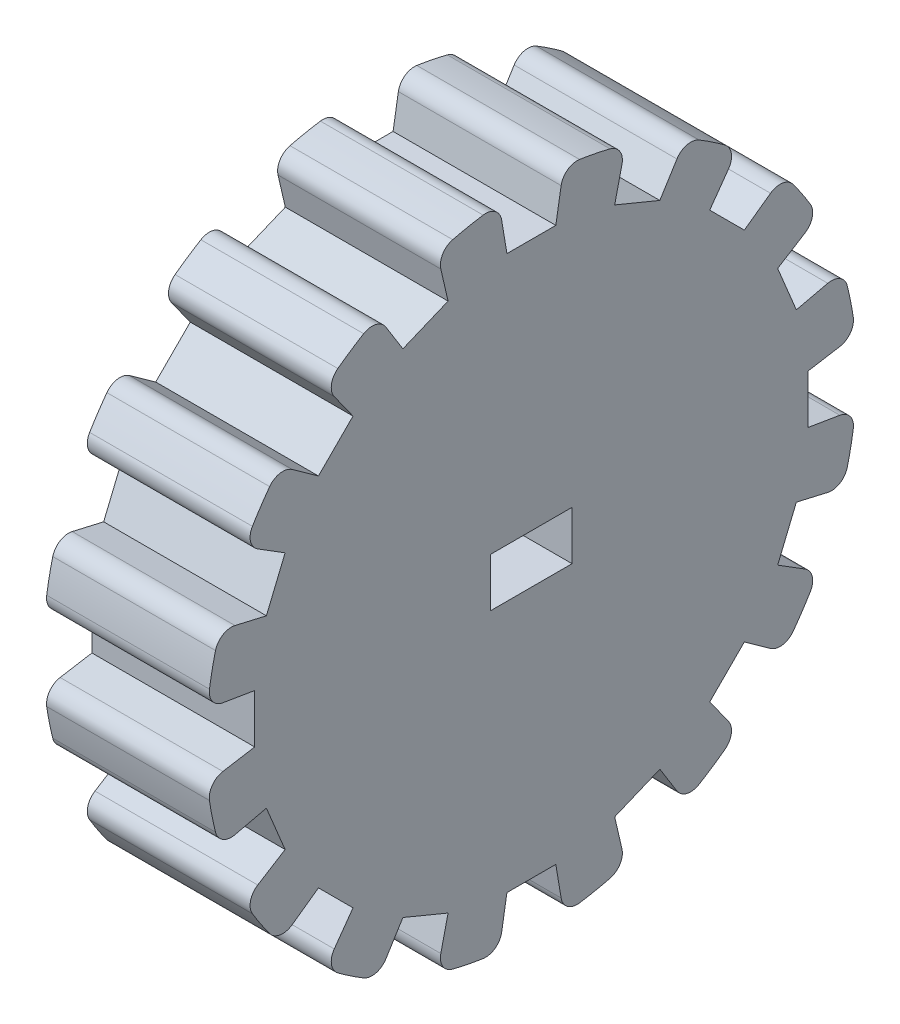
SolidWorks part; units mm, degrees
ref_plane "Front Plane" through (0, 0, 0) normal (0, 0, 1) x (1, 0, 0)
ref_plane "Top Plane" through (0, 0, 0) normal (0, 1, 0) x (1, 0, 0)
ref_plane "Right Plane" through (0, 0, 0) normal (1, 0, 0) x (0, 0, -1)
sketch "Sketch1" plane through (0, 0, 0) normal (0, 0, 1) x (1, 0, 0)
  line L0 (0, 0) -> (-34.486, 0) construction
  line L1 (0, 0) -> (-10, 0)
  line L2 (-10, 0) -> (-10, 5)
  line L3 (-10, 10) -> (-10, 5)
  line L4 (0, 20) -> (0, 5)
  line L6 (-10, 10) -> (-10, 20)
  line L7 (-10, 20) -> (0, 20)
  line L12 (0, 5) -> (0, 0)
  dimension "D1" = 20
  dimension "D2" = 20
  dimension "D3" = 10
  dimension "D5" = 5
  dimension "D6" = 10
revolve "Revolve1" add sketch "Sketch1" angle 360 about L0
sketch "Sketch4" plane through (-10, 0, 0) normal (-1, 0, 0) x (0, 0, 1)
  line L1 (2.5, -1.5) -> (-2.5, -1.5)
  line L6 (2.5, -1.5) -> (2.5, 1.5)
  line L7 (2.5, 1.5) -> (-2.5, 1.5)
  line L8 (-2.5, -1.5) -> (-2.5, 1.5)
  line L9 (2.5, -1.5) -> (-2.5, 1.5) construction
  line L10 (2.5, 1.5) -> (-2.5, -1.5) construction
  point P0 (0, 0)
  point P3 (0, 0)
  point P8 (0, 0)
  dimension "D1" = 3
  dimension "D2" = 5
extrude "Cut-Extrude2" cut sketch "Sketch4" against normal blind 10
sketch "Sketch5" plane through (0, 0, 0) normal (1, 0, 0) x (0, 0, -1)
  line L0 (-2.502, 23) -> (2.502, 23)
  line L1 (-1.5018, 17) -> (1.5018, 17)
  line L2 (-2.502, 23) -> (-1.5018, 17)
  line L3 (2.502, 23) -> (1.5018, 17)
  point P0 (0, 0)
  point P6 (0, 17)
  dimension "D1" = 6
  dimension "D2" = 17
extrude "Cut-Extrude3" cut sketch "Sketch5" against normal blind 10
fillet "Fillet1" radius 1 2 edges at (-5, 19.9012, -1.9854) (-5, 19.9012, 1.9854)
pattern_circular "CirPattern1" count 16 over 360 about axis through (0, 0, 0) along (1, 0, 0) of "Fillet1", "Cut-Extrude3"
